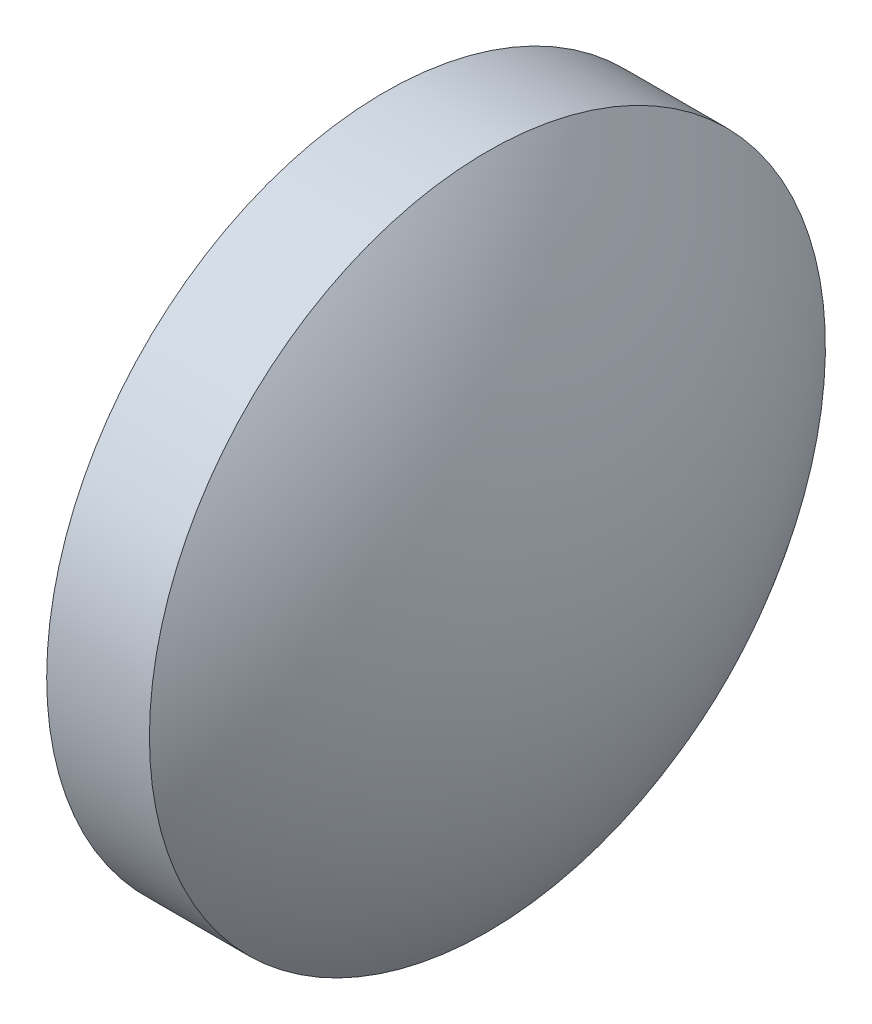
SolidWorks part; units mm, degrees
ref_plane "前视基准面" through (0, 0, 0) normal (0, 0, 1) x (1, 0, 0)
ref_plane "上视基准面" through (0, 0, 0) normal (0, 1, 0) x (1, 0, 0)
ref_plane "右视基准面" through (0, 0, 0) normal (1, 0, 0) x (0, 0, -1)
sketch "草图2" plane through (0, 0, 0) normal (0, 0, 1) x (1, 0, 0)
  line L0 (522.208, 17.0546) -> (527.8085, 17.0546) construction
  line L1 (523.0056, 17.0546) -> (523.0056, 22.0546)
  line L2 (526.2056, 17.0546) -> (523.0056, 17.0546)
  line L5 (523.0056, 22.0546) -> (524.5256, 22.0546)
  arc A0 (526.2056, 17.0546) -> (524.5256, 22.0546) centre (517.9252, 17.0546) ccw
revolve "旋转2" add sketch "草图2" angle 360 about L0
